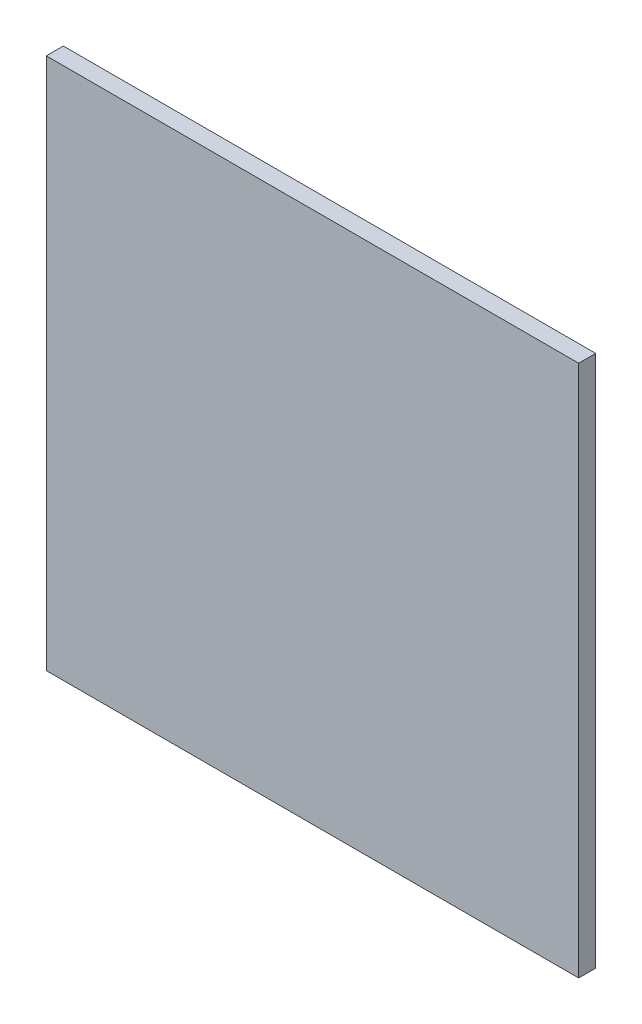
SolidWorks part; units mm, degrees
ref_plane "Front Plane" through (0, 0, 0) normal (0, 0, 1) x (1, 0, 0)
ref_plane "Top Plane" through (0, 0, 0) normal (0, 1, 0) x (1, 0, 0)
ref_plane "Right Plane" through (0, 0, 0) normal (1, 0, 0) x (0, 0, -1)
sketch "Sketch1" plane through (0, 0, 0) normal (0, 0, 1) x (1, 0, 0)
  line L1 (-50, -50) -> (50, -50)
  line L2 (-50, -50) -> (-50, 50)
  line L3 (-50, 50) -> (50, 50)
  line L4 (50, -50) -> (50, 50)
  line L5 (-50, -50) -> (50, 50) construction
  line L6 (-50, 50) -> (50, -50) construction
  point P0 (0, 0)
  dimension "D1" = 100
  dimension "D2" = 100
extrude "Boss-Extrude1" add sketch "Sketch1" along normal blind 3.2
